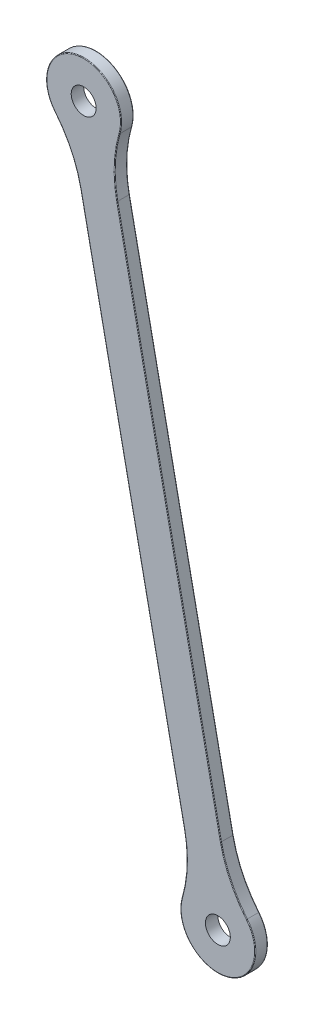
SolidWorks part; units mm, degrees
ref_plane "Front Plane" through (0, 0, 0) normal (0, 0, 1) x (1, 0, 0)
ref_plane "Top Plane" through (0, 0, 0) normal (0, 1, 0) x (1, 0, 0)
ref_plane "Right Plane" through (0, 0, 0) normal (1, 0, 0) x (0, 0, -1)
sketch "Sketch1" plane through (0, 0, 0) normal (0, 0, 1) x (1, 0, 0)
  line L0 (33.7783, 57.1554) -> (1.4673, 213.8589) construction
  line L1 (33.7783, 57.1554) -> (1.4673, 213.8589) construction
  line L2 (33.7783, 57.1554) -> (1.4673, 213.8589) construction
  line L3 (29.371, 56.2466) -> (-2.94, 212.9502)
  line L4 (38.1856, 58.0641) -> (5.8746, 214.7677)
  arc A0 (7.4486, 207.134) -> (-1.366, 205.3165) centre (1.4673, 213.8589) ccw
  arc A1 (27.797, 63.8803) -> (36.6116, 65.6978) centre (33.7783, 57.1554) ccw
  arc A2 (29.371, 56.2466) -> (38.1856, 58.0641) centre (33.7783, 57.1554) ccw
  arc A3 (5.8746, 214.7677) -> (-2.94, 212.9502) centre (1.4673, 213.8589) ccw
  arc A4 (-2.94, 212.9502) -> (5.8746, 214.7677) centre (1.4673, 213.8589) ccw
  arc A5 (29.371, 56.2466) -> (38.1856, 58.0641) centre (33.7783, 57.1554) cw
  point P5 (17.6228, 135.5072)
  dimension "D1" = 18
  dimension "D2" = 9
extrude "Boss-Extrude1" add sketch "Sketch1" against normal blind 3 contours A3 L4 A0 L3 | L3 A5 L4 A4 | A2 L3 A1 L4
fillet "Fillet1" radius 30 4 edges at (36.6116, 65.6978, -1.5) (27.797, 63.8803, -1.5) (-1.366, 205.3165, -1.5) (7.4486, 207.134, -1.5)
fillet "Fillet2" radius 0.15 20 edges at (38.2783, 57.1554, -3) (38.2783, 57.1554, 0) (5.9673, 213.8589, -3) (5.9673, 213.8589, 0) (-1.5826, 202.0183, -3) (-1.5826, 202.0183, 0) (-0.3502, 222.6735, -3) (-0.3502, 222.6735, 0) (8.9523, 204.1905, -3) (8.9523, 204.1905, 0) (22.0301, 136.4159, 0) (22.0301, 136.4159, -3) (36.8283, 68.996, -3) (36.8283, 68.996, 0) (35.5958, 48.3408, -3) (35.5958, 48.3408, 0) (26.2934, 66.8238, -3) (26.2934, 66.8238, 0) (13.2155, 134.5984, -3) (13.2155, 134.5984, 0)
sketch "Sketch2" plane through (0, 0, 0) normal (0, 0, 1) x (1, 0, 0)
  circle A0 centre (1.4673, 213.8589) radius 3
  circle A1 centre (33.7783, 57.1554) radius 3
  circle A2 centre (1.4673, 213.8589) radius 4.65 construction
  circle A3 centre (1.4673, 213.8589) radius 4.65
  circle A4 centre (33.7783, 57.1554) radius 4.65 construction
  circle A5 centre (33.7783, 57.1554) radius 4.65
  dimension "D1" = 6
extrude "Boss-Extrude2" add sketch "Sketch2" against normal up to surface (3 mm away) up to face at (38.4283, 57.1554, -3)
